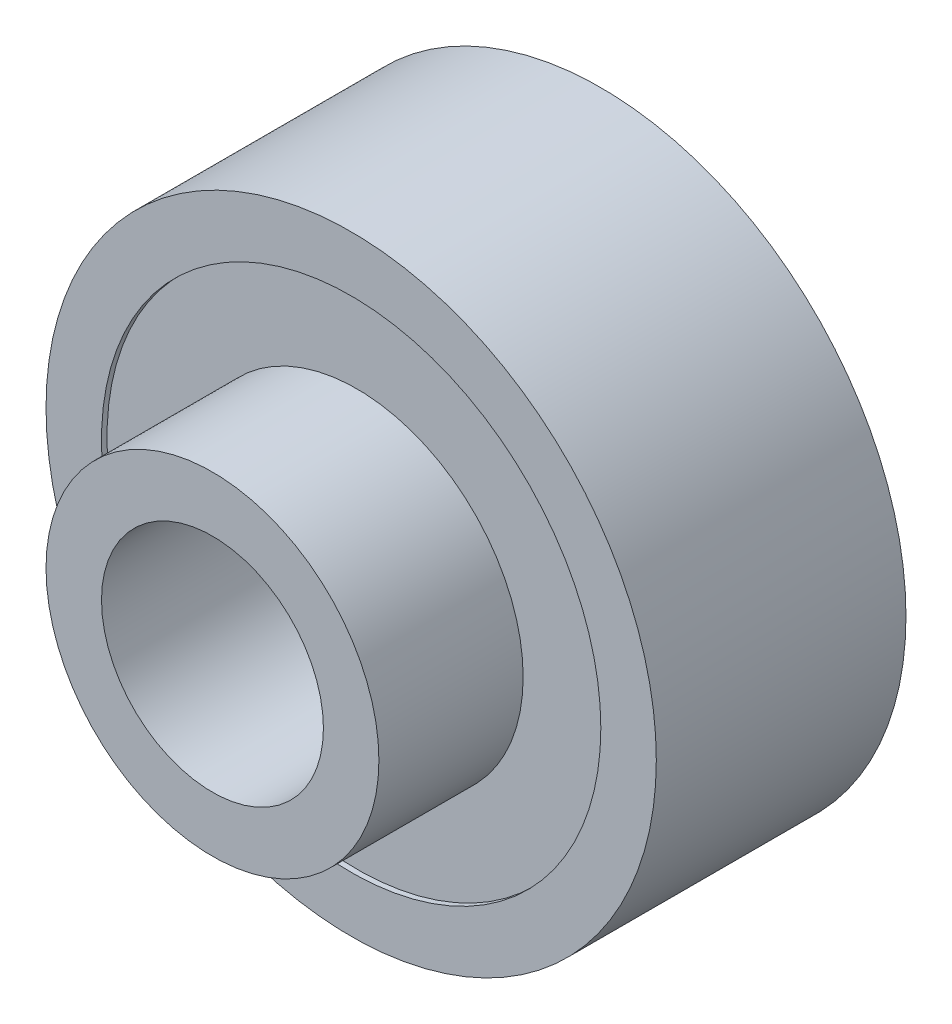
SolidWorks part; units mm, degrees
ref_plane "Front Plane" through (0, 0, 0) normal (0, 0, 1) x (1, 0, 0)
ref_plane "Top Plane" through (0, 0, 0) normal (0, 1, 0) x (1, 0, 0)
ref_plane "Right Plane" through (0, 0, 0) normal (1, 0, 0) x (0, 0, -1)
sketch "Sketch1" plane through (0, 0, 0) normal (0, 0, 1) x (1, 0, 0)
  circle A0 centre (0, 0) radius 11
  dimension "D1" = 22
extrude "Boss-Extrude1" add sketch "Sketch1" along normal blind 9
sketch "Sketch2" plane through (0, 0, 9) normal (0, 0, 1) x (1, 0, 0)
  circle A0 centre (0, 0) radius 4
  dimension "D1" = 8
extrude "Cut-Extrude1" cut sketch "Sketch2" against normal through all
sketch "Sketch3" plane through (0, 0, 9) normal (0, 0, 1) x (1, 0, 0)
  circle A0 centre (0, 0) radius 6
  circle A1 centre (0, 0) radius 9
  point P4 (0, 0)
  dimension "D1" = 18
  dimension "D2" = 12
extrude "Cut-Extrude2" cut sketch "Sketch3" against normal blind 0.2
sketch "Sketch4" plane through (0, 0, 0) normal (0, 0, -1) x (-1, 0, 0)
  circle A0 centre (0, 0) radius 6
  circle A1 centre (0, 0) radius 9
  dimension "D1" = 18
  dimension "D2" = 12
extrude "Cut-Extrude3" cut sketch "Sketch4" against normal blind 0.2
sketch "Sketch5" plane through (0, 0, 9) normal (0, 0, 1) x (1, 0, 0)
  circle A0 centre (0, 0) radius 4
  circle A1 centre (0, 0) radius 6
  dimension "D1" = 8
  dimension "D2" = 12
extrude "Boss-Extrude2" add sketch "Sketch5" along normal blind 5
